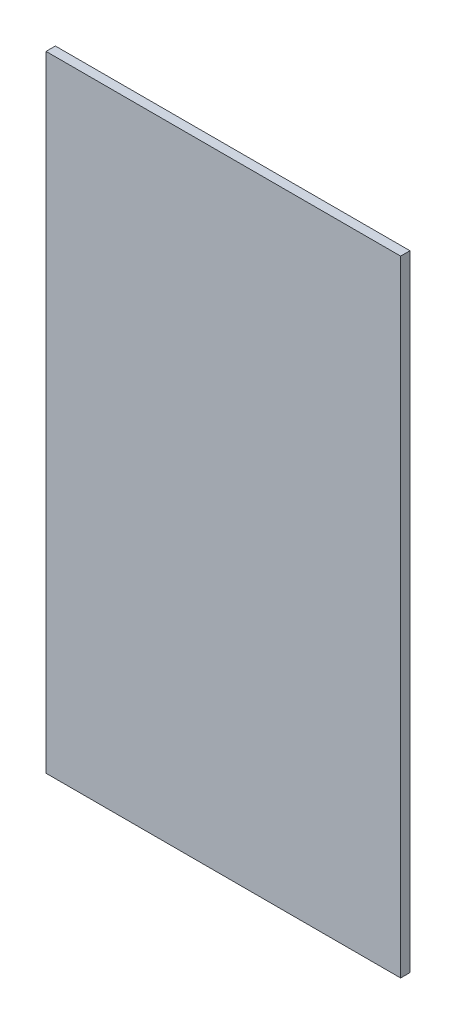
SolidWorks part; units mm, degrees
ref_plane "Plan de face" through (0, 0, 0) normal (0, 0, 1) x (1, 0, 0)
ref_plane "Plan de dessus" through (0, 0, 0) normal (0, 1, 0) x (1, 0, 0)
ref_plane "Plan de droite" through (0, 0, 0) normal (1, 0, 0) x (0, 0, -1)
sketch "Esquisse1" plane through (0, 0, 0) normal (0, 0, 1) x (1, 0, 0)
  line L1 (-190, 335) -> (190, 335)
  line L2 (-190, 335) -> (-190, -335)
  line L3 (-190, -335) -> (190, -335)
  line L4 (190, 335) -> (190, -335)
  dimension "D1" = 380
  dimension "D2" = 670
  dimension "D3" = 335
  dimension "D4" = 190
extrude "Boss.-Extru.1" add sketch "Esquisse1" along normal blind 10
